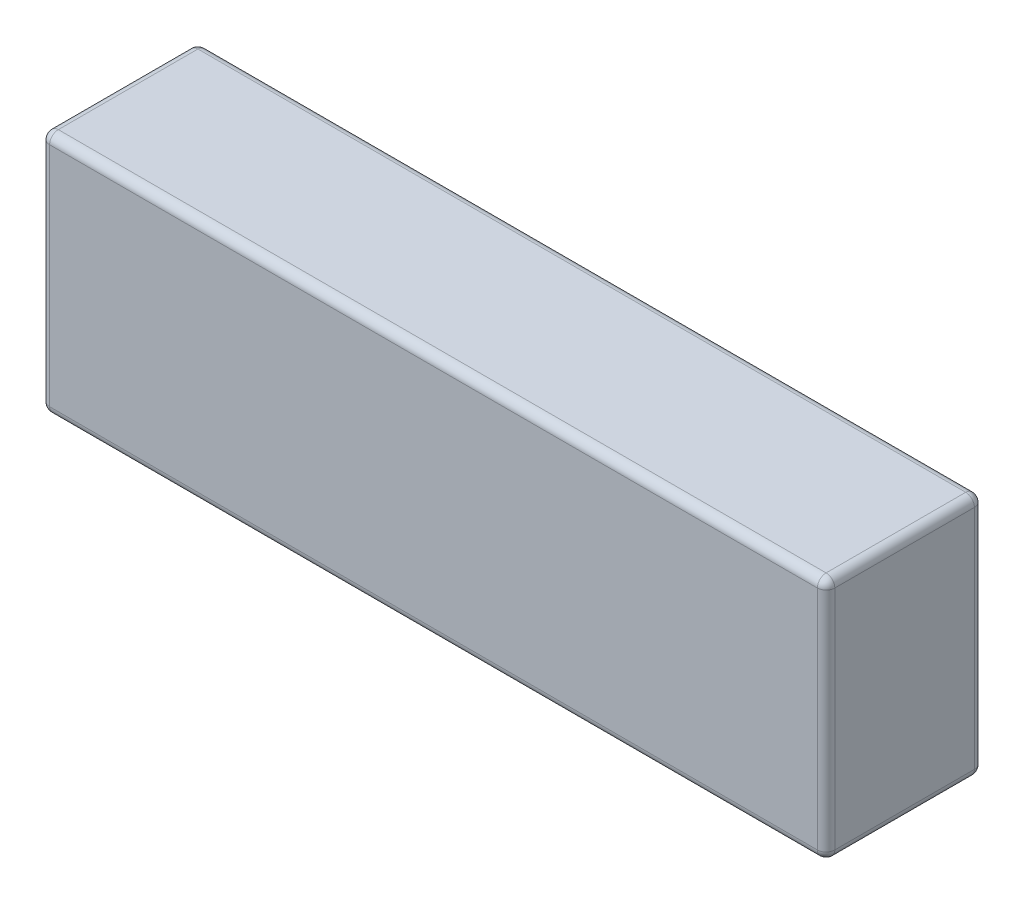
SolidWorks part; units mm, degrees
ref_plane "Piano frontale" through (0, 0, 0) normal (0, 0, 1) x (1, 0, 0)
ref_plane "Piano superiore" through (0, 0, 0) normal (0, 1, 0) x (1, 0, 0)
ref_plane "Piano destro" through (0, 0, 0) normal (1, 0, 0) x (0, 0, -1)
sketch "Schizzo1" plane through (0, 0, 0) normal (0, 1, 0) x (1, 0, 0)
  line L0 (0, -9) -> (0, 9) construction
  line L1 (-45, 9) -> (45, 9)
  line L2 (-45, 9) -> (-45, -9)
  line L3 (-45, -9) -> (45, -9)
  line L4 (45, 9) -> (45, -9)
  point P6 (0, 0)
  dimension "D1" = 90
  dimension "D2" = 18
extrude "Estrusione-Estrusione1" add sketch "Schizzo1" along normal blind 28
fillet "Raccordo1" radius 1 12 edges at (-45, 0, 0) (45, 0, 0) (45, 28, 0) (-45, 28, 0) (45, 14, -9) (0, 28, -9) (-45, 14, -9) (0, 0, -9) (-45, 14, 9) (0, 28, 9) (45, 14, 9) (0, 0, 9)
